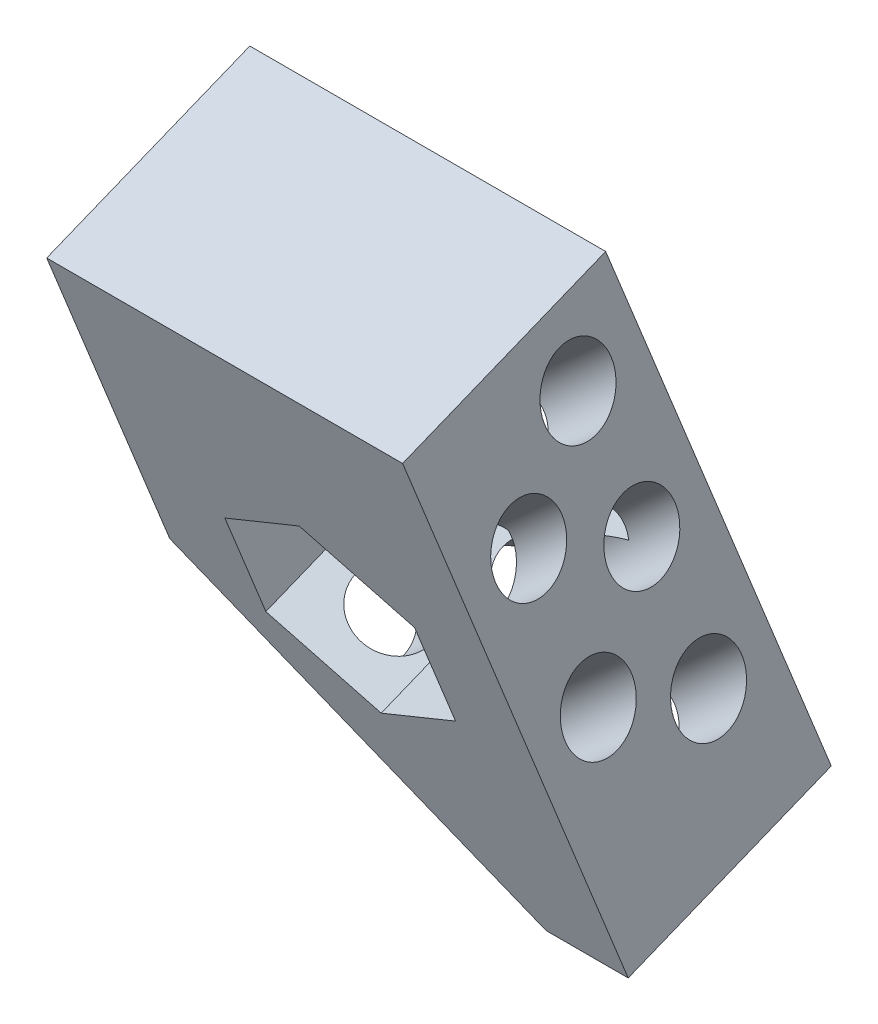
SolidWorks part; units mm, degrees
ref_plane "Front Plane" through (0, 0, 0) normal (0, 0, 1) x (1, 0, 0)
ref_plane "Top Plane" through (0, 0, 0) normal (0, 1, 0) x (1, 0, 0)
ref_plane "Right Plane" through (0, 0, 0) normal (1, 0, 0) x (0, 0, -1)
sketch "Sketch4" plane through (0, 0, 0) normal (0, 1, 0) x (1, 0, 0)
  line L0 (0, 0) -> (109.7326, 68.5685) construction
  line L1 (0, 0) -> (98.9344, 0) construction
  dimension "D1" = 32
ref_plane "Plane1" through (0, 0, 0) normal (0, -1, 0) x (0.848, 0, -0.5299)
ref_plane "Plane2" through (0, 0, 0) normal (0, 0.3746, -0.9272) x (1, 0, 0)
sketch "Sketch1" plane through (0, 0, 0) normal (0, 0.3746, -0.9272) x (0, -0.9272, -0.3746)
  line L1 (0, 0) -> (110, 0)
  line L2 (0, 0) -> (0, 65)
  line L3 (0, 65) -> (110, 65)
  line L4 (110, 0) -> (110, 65)
  dimension "D1" = 65
  dimension "D2" = 110
extrude "Boss-Extrude1" add sketch "Sketch1" along normal blind 40
chamfer "Chamfer1" distance 50 angle 45 1 edges at (-65, -94.4981, -59.7504)
sketch "Sketch2" plane through (-62.5, -57.949, -23.4129) normal (-0.7071, -0.6556, -0.2649) x (0.1942, 0.1801, -0.9643)
  line L3 (25.9516, -11.0911) -> (45.3758, 56.8994) construction
  line L4 (37.49, -14.3875) -> (-0.9712, -3.3995) construction
  line L5 (18.453, 64.5909) -> (56.9142, 53.603) construction
  line L6 (56.9142, 53.603) -> (37.49, -14.3875) construction
  line L7 (10.5672, -6.6959) -> (29.9913, 61.2945) construction
  line L8 (37.49, -14.3875) -> (25.9516, -11.0911) construction
  line L9 (10.5672, -6.6959) -> (-0.9712, -3.3995) construction
  line L10 (-0.9712, -3.3995) -> (18.453, 64.5909) construction
  circle A0 centre (24.3021, 41.3806) radius 6.5
  circle A1 centre (36.1155, 24.4855) radius 6.5
  circle A2 centre (17.7093, 18.3039) radius 6.5
  circle A3 centre (30.0721, 3.3319) radius 6.5
  circle A4 centre (42.4336, 46.6007) radius 6.5
  dimension "D1" = 12
  dimension "D2" = 15
  dimension "D3" = 37
  dimension "D4" = 60
  dimension "D5" = 26
  dimension "D7" = 13
  dimension "D6" = 50
extrude "Cut-Extrude1" cut sketch "Sketch2" against normal through all
sketch "Sketch3" plane through (0, 14.9843, -37.0874) normal (0, 0.3746, -0.9272) x (0, -0.9272, -0.3746)
  line L0 (0, 0) -> (110, 0) construction
  line L1 (45, 14.6795) -> (65, 14.6795)
  line L2 (65, 14.6795) -> (75, 32)
  line L3 (75, 32) -> (65, 49.3205)
  line L4 (65, 49.3205) -> (45, 49.3205)
  line L5 (45, 49.3205) -> (35, 32)
  line L6 (35, 32) -> (45, 14.6795)
  line L7 (0, 65) -> (0, 0) construction
  circle A0 centre (55, 32) radius 17.3205 construction
  dimension "D1" = 20
  dimension "D2" = 55
  dimension "D3" = 32
extrude "Cut-Extrude2" cut sketch "Sketch3" against normal through all
